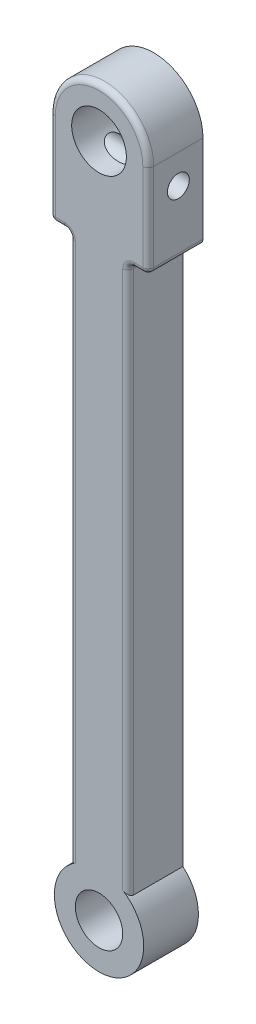
SolidWorks part; units mm, degrees
ref_plane "Front Plane" through (0, 0, 0) normal (0, 0, 1) x (1, 0, 0)
ref_plane "Top Plane" through (0, 0, 0) normal (0, 1, 0) x (1, 0, 0)
ref_plane "Right Plane" through (0, 0, 0) normal (1, 0, 0) x (0, 0, -1)
sketch "Sketch1" plane through (0, 0, 0) normal (0, 0, 1) x (1, 0, 0)
  line L0 (0, 0) -> (0, -185) construction
  line L1 (-13.5, 0) -> (-13.5, -24)
  line L2 (-8, -175.723) -> (-8, -27)
  line L3 (-12, -25.5) -> (-9.5, -25.5)
  line L4 (12, -25.5) -> (9.5, -25.5)
  line L5 (13.5, 0) -> (13.5, -24)
  line L6 (8, -175.723) -> (8, -27)
  line L7 (0, -178.5) -> (0, -185) construction
  arc A1 (13.5, 0) -> (-13.5, 0) centre (0, 0) ccw
  circle A2 centre (0, -185) radius 6.5
  arc A3 (-8, -175.723) -> (8, -175.723) centre (0, -185) ccw
  arc A4 (-8, -27) -> (-9.5, -25.5) centre (-9.5, -27) ccw
  arc A5 (-13.5, -24) -> (-12, -25.5) centre (-12, -24) ccw
  arc A6 (13.5, -24) -> (12, -25.5) centre (12, -24) cw
  arc A7 (8, -27) -> (9.5, -25.5) centre (9.5, -27) cw
  circle A8 centre (0, 0) radius 7.5
  point P15 (-13.5, -25.5)
  dimension "D1" = 15
  dimension "D2" = 13
  dimension "D3" = 24.5
  dimension "D4" = 27
  dimension "D5" = 185
  dimension "D8" = 1.5
  dimension "D9" = 13.5
  dimension "D10" = 2.5
  dimension "D6" = 16
  dimension "D7" = 25.5
  dimension "D12" = 16
extrude "Boss-Extrude1" add sketch "Sketch1" along normal blind 15
fillet "Fillet2" radius 1.5 11 edges at (10.75, -25.5, 15) (8, -101.3615, 15) (8.4393, -25.9393, 15) (-8, -101.3615, 15) (-8.4393, -25.9393, 15) (-10.75, -25.5, 15) (-13.0607, -25.0607, 15) (-13.5, -12, 15) (0, 13.5, 15) (13.5, -12, 15) (13.0607, -25.0607, 15)
sketch "Sketch4" plane through (13.5, 0, 0) normal (1, 0, 0) x (0, 0, -1)
  line L1 (-13.5, 0) -> (0, 0) construction
  circle A0 centre (-6.75, -8) radius 3
  point P5 (-6.75, 0)
  dimension "D1" = 6
  dimension "D2" = 8
extrude "Cut-Extrude1" cut sketch "Sketch4" against normal through all
